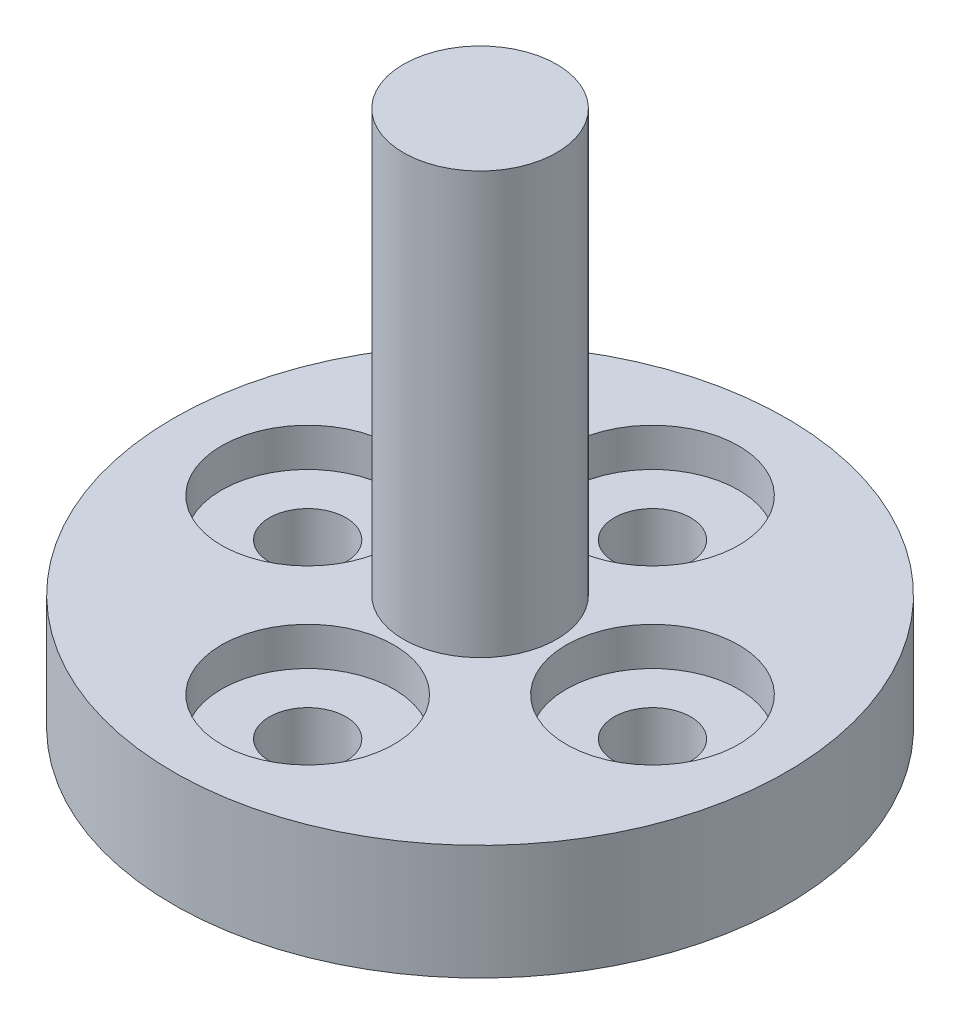
SolidWorks part; units mm, degrees
ref_plane "Front Plane" through (0, 0, 0) normal (0, 0, 1) x (1, 0, 0)
ref_plane "Top Plane" through (0, 0, 0) normal (0, 1, 0) x (1, 0, 0)
ref_plane "Right Plane" through (0, 0, 0) normal (1, 0, 0) x (0, 0, -1)
sketch "Sketch1" plane through (0, 0, 0) normal (0, 0, 1) x (1, 0, 0)
  line L0 (0, 0) -> (8, 0)
  line L1 (8, 0) -> (8, 3)
  line L2 (8, 3) -> (2, 3)
  line L3 (2, 3) -> (2, 14)
  line L4 (2, 14) -> (0, 14)
  line L5 (0, 14) -> (0, 0)
  dimension "D1" = 8
  dimension "D2" = 14
  dimension "D3" = 2
  dimension "D4" = 11
revolve "Revolve1" add sketch "Sketch1" angle 360 about L5
sketch "Sketch2" plane through (0, 3, 0) normal (0, 1, 0) x (1, 0, 0)
  circle A0 centre (0, 0) radius 4.5
  dimension "D1" = 9
sketch "Sketch3" plane through (0, 3, 0) normal (0, 1, 0) x (1, 0, 0)
  circle A0 centre (0, 4.5) radius 1
  circle A1 centre (0, 0) radius 4.5 construction
  circle A2 centre (4.5, 0) radius 1
  circle A3 centre (0, -4.5) radius 1
  circle A4 centre (-4.5, 0) radius 1
  point P13 (0, 0)
  dimension "D1" = 2
  dimension "D2" = 4
extrude "Cut-Extrude1" cut sketch "Sketch3" against normal through all
sketch "Sketch4" plane through (0, 3, 0) normal (0, 1, 0) x (1, 0, 0)
  circle A0 centre (0, 4.5) radius 2.25
  circle A1 centre (4.5, 0) radius 2.25
  circle A2 centre (0, -4.5) radius 2.25
  circle A3 centre (-4.5, 0) radius 2.25
  point P12 (0, 0)
  dimension "D1" = 4.5
  dimension "D2" = 4
extrude "Cut-Extrude2" cut sketch "Sketch4" against normal blind 1
